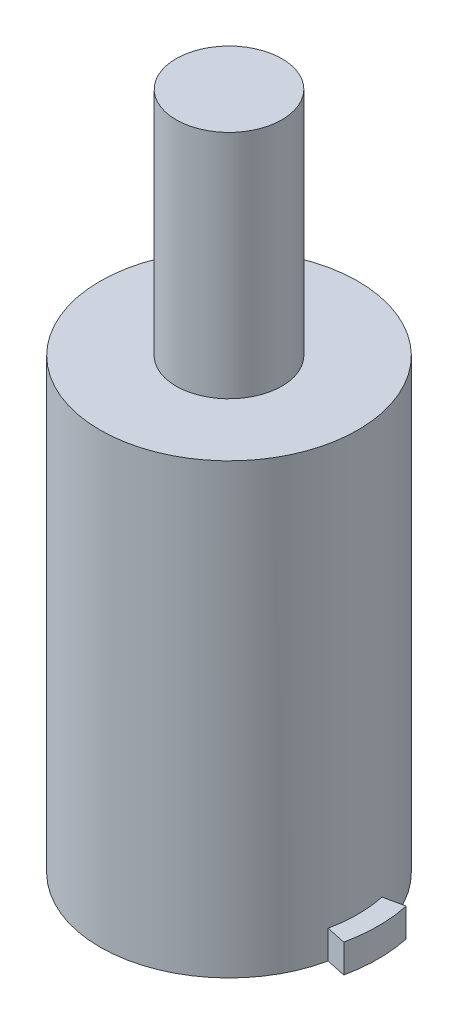
SolidWorks part; units mm, degrees
ref_plane "Front Plane" through (0, 0, 0) normal (0, 0, 1) x (1, 0, 0)
ref_plane "Top Plane" through (0, 0, 0) normal (0, 1, 0) x (1, 0, 0)
ref_plane "Right Plane" through (0, 0, 0) normal (1, 0, 0) x (0, 0, -1)
sketch "Sketch1" plane through (0, 0, 0) normal (0, 1, 0) x (1, 0, 0)
  circle A0 centre (0, 0) radius 4.75
  dimension "D1" = 9.5
extrude "Boss-Extrude1" add sketch "Sketch1" along normal blind 16.5
sketch "Sketch2" plane through (0, 16.5, 0) normal (0, 1, 0) x (1, 0, 0)
  circle A0 centre (0, 0) radius 1.95
  dimension "D1" = 3.9
extrude "Boss-Extrude2" add sketch "Sketch2" along normal blind 8.5
sketch "Sketch3" plane through (0, 0, 0) normal (0, -1, 0) x (1, 0, 0)
  line L0 (-5.3784, 1.15) -> (0, 0) construction
  line L1 (0, 0) -> (-5.5, 0) construction
  line L2 (0, 0) -> (0, 5.5) construction
  line L3 (-5.3784, -1.15) -> (0, 0) construction
  line L4 (-5.3784, 1.15) -> (-4.645, 0.9932)
  line L5 (-4.645, -0.9932) -> (-5.3784, -1.15)
  line L6 (4.645, -0.9932) -> (5.3784, -1.15)
  line L7 (5.3784, 1.15) -> (4.645, 0.9932)
  circle A0 centre (0, 0) radius 5.5 construction
  arc A1 (-5.3784, 1.15) -> (-5.3784, -1.15) centre (0, 0) ccw
  arc A2 (-4.645, 0.9932) -> (-4.645, -0.9932) centre (0, 0) ccw
  circle A3 centre (0, 0) radius 4.75 construction
  arc A4 (4.645, 0.9932) -> (4.645, -0.9932) centre (0, 0) cw
  arc A5 (5.3784, 1.15) -> (5.3784, -1.15) centre (0, 0) cw
  dimension "D1" = 11
  dimension "D2" = 2.3
extrude "Boss-Extrude3" add sketch "Sketch3" against normal blind 1.05
sketch "Sketch4" plane through (0, 0, 0) normal (0, -1, 0) x (1, 0, 0)
  line L0 (-5.5, 0) -> (5.5, 0) construction
  arc A0 (-5.3784, 1.15) -> (-5.3784, -1.15) centre (0, 0) ccw construction
  arc A1 (5.3784, -1.15) -> (5.3784, 1.15) centre (0, 0) ccw construction
